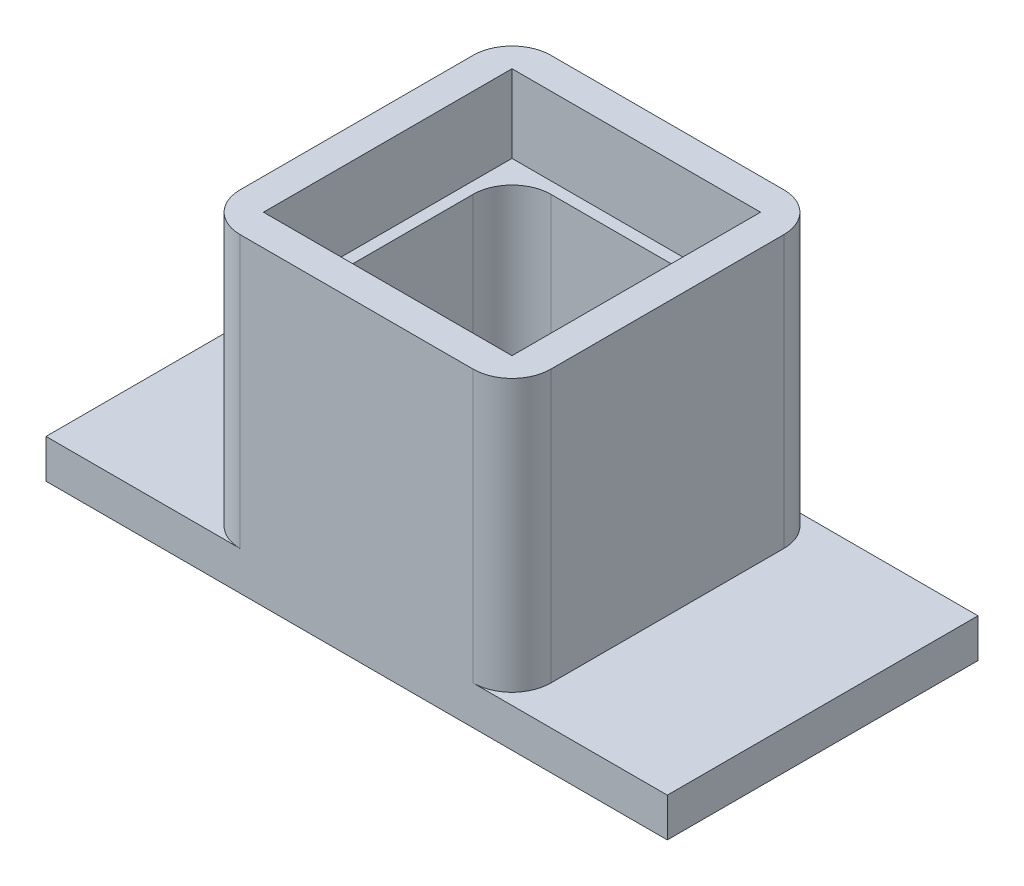
SolidWorks part; units mm, degrees
ref_plane "Front Plane" through (0, 0, 0) normal (0, 0, 1) x (1, 0, 0)
ref_plane "Top Plane" through (0, 0, 0) normal (0, 1, 0) x (1, 0, 0)
ref_plane "Right Plane" through (0, 0, 0) normal (1, 0, 0) x (0, 0, -1)
sketch "Sketch1" plane through (0, 0, 0) normal (0, 1, 0) x (1, 0, 0)
  line L0 (34.5, 5.5) -> (34.5, 34.5)
  line L1 (0, 0) -> (40, 0)
  line L2 (0, 0) -> (0, 40)
  line L3 (0, 40) -> (40, 40)
  line L4 (40, 0) -> (40, 40)
  line L5 (5.5, 34.5) -> (34.5, 34.5)
  line L6 (5.5, 5.5) -> (5.5, 34.5)
  line L7 (5.5, 5.5) -> (34.5, 5.5)
  dimension "D1" = 40
  dimension "D2" = 5.5
extrude "Boss-Extrude1" add sketch "Sketch1" along normal blind 25
sketch "Sketch2" plane through (0, 25, 0) normal (0, 1, 0) x (1, 0, 0)
  line L0 (36, 36) -> (36, 4)
  line L1 (0, 40) -> (40, 40)
  line L2 (0, 40) -> (0, 0)
  line L3 (0, 0) -> (40, 0)
  line L4 (40, 40) -> (40, 0)
  line L5 (4, 4) -> (36, 4)
  line L6 (4, 36) -> (4, 4)
  line L7 (4, 36) -> (36, 36)
  dimension "D1" = 4
extrude "Boss-Extrude2" add sketch "Sketch2" along normal blind 10
sketch "Sketch4" plane through (0, 0, 0) normal (0, -1, 0) x (1, 0, 0)
  line L0 (40, -40) -> (0, -40) construction
  line L1 (-20, 0) -> (60, 0)
  line L2 (-20, 0) -> (-20, -40)
  line L3 (-20, -40) -> (60, -40)
  line L4 (60, 0) -> (60, -40)
  line L5 (0, 0) -> (40, 0) construction
  line L6 (0, -40) -> (0, 0) construction
  line L7 (40, 0) -> (40, -40) construction
  line L8 (34.5, -5.5) -> (34.5, -34.5) construction
  line L9 (5.5, -5.5) -> (34.5, -5.5)
  line L10 (5.5, -5.5) -> (5.5, -34.5)
  line L11 (5.5, -34.5) -> (34.5, -34.5)
  line L12 (34.5, -5.5) -> (34.5, -34.5)
  dimension "D1" = 20
  dimension "D2" = 20
extrude "Boss-Extrude3" add sketch "Sketch4" along normal blind 5
fillet "Fillet6" radius 5 8 edges at (5.5, 10, -34.5) (5.5, 10, -5.5) (34.5, 10, -5.5) (34.5, 10, -34.5) (40, 17.5, 0) (40, 17.5, -40) (0, 17.5, -40) (0, 17.5, 0)
